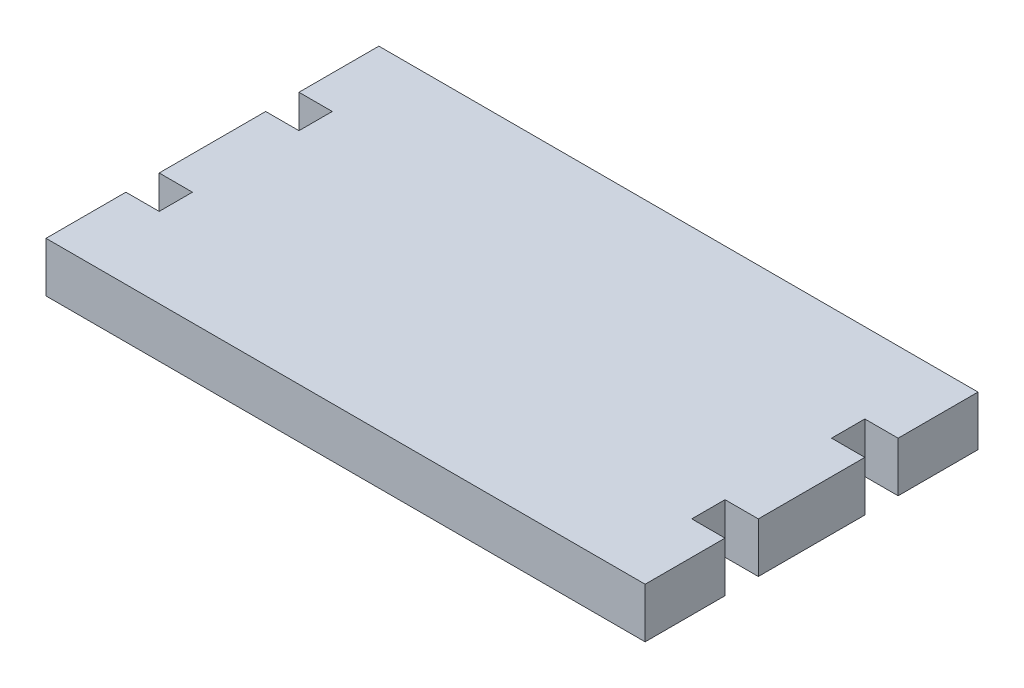
SolidWorks part; units mm, degrees
ref_plane "Front Plane" through (0, 0, 0) normal (0, 0, 1) x (1, 0, 0)
ref_plane "Top Plane" through (0, 0, 0) normal (0, 1, 0) x (1, 0, 0)
ref_plane "Right Plane" through (0, 0, 0) normal (1, 0, 0) x (0, 0, -1)
sketch "Sketch1" plane through (0, 0, 0) normal (0, 1, 0) x (1, 0, 0)
  line L4 (0, 24.13) -> (3.175, 24.13)
  line L5 (0, 0) -> (57.15, 0)
  line L6 (0, 0) -> (0, 7.62)
  line L7 (0, 31.75) -> (57.15, 31.75)
  line L9 (3.175, 24.13) -> (3.175, 20.955)
  line L10 (3.175, 20.955) -> (0, 20.955)
  line L11 (0, 20.955) -> (0, 10.795)
  line L12 (0, 10.795) -> (3.175, 10.795)
  line L13 (3.175, 10.795) -> (3.175, 7.62)
  line L14 (3.175, 7.62) -> (0, 7.62)
  line L15 (57.15, 24.13) -> (53.975, 24.13)
  line L16 (53.975, 24.13) -> (53.975, 20.955)
  line L17 (53.975, 20.955) -> (57.15, 20.955)
  line L18 (57.15, 20.955) -> (57.15, 10.795)
  line L19 (57.15, 7.62) -> (53.975, 7.62)
  line L20 (53.975, 7.62) -> (53.975, 10.795)
  line L21 (53.975, 10.795) -> (57.15, 10.795)
  line L22 (57.15, 7.62) -> (57.15, 0)
  line L23 (57.15, 31.75) -> (57.15, 24.13)
  line L24 (0, 24.13) -> (0, 31.75)
  line L25 (0, 10.795) -> (0, 20.955)
  point P4 (41.687, 24.684)
  dimension "D1" = 7.62
  dimension "D2" = 31.75
  dimension "D3" = 3.175
  dimension "D4" = 3.175
  dimension "D5" = 3.175
  dimension "D6" = 3.175
  dimension "D7" = 7.62
  dimension "D8" = 3.175
  dimension "D9" = 57.15
  dimension "D10" = 3.175
  dimension "D11" = 3.175
extrude "Boss-Extrude1" add sketch "Sketch1" along normal blind 4.7625 contours L24 L4 L9 L10 L11 L12 L13 L14 L6 L5 L22 L19 L20 L21 L18 L17 L16 L15 L23 L7
